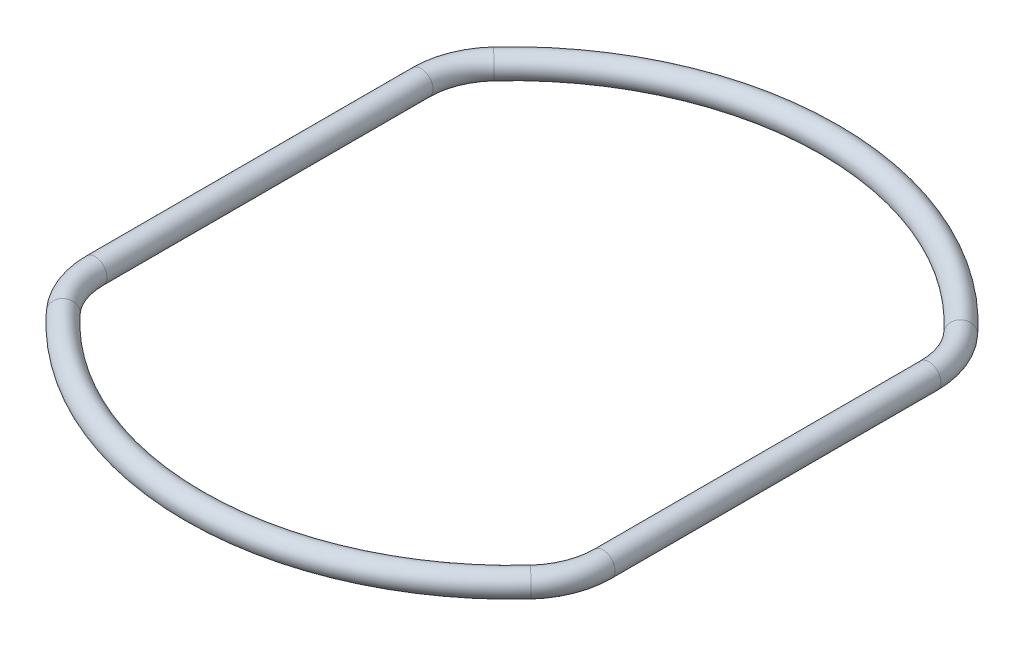
SolidWorks part; units mm, degrees
ref_plane "Vorne" through (0, 0, 0) normal (0, 0, 1) x (1, 0, 0)
ref_plane "Oben" through (0, 0, 0) normal (0, 1, 0) x (1, 0, 0)
ref_plane "Rechts" through (0, 0, 0) normal (1, 0, 0) x (0, 0, -1)
sketch "Skizze1" plane through (0, 0, 0) normal (0, 1, 0) x (1, 0, 0)
  line L0 (0, 82.4427) -> (0, -82.4427) construction
  line L2 (65.9318, -42.3008) -> (65.9318, 42.3008) construction
  line L4 (-65.9318, -42.3008) -> (-65.9318, 42.3008)
  line L5 (65.9318, -49.4954) -> (-65.9318, 49.4954) construction
  line L6 (65.9318, 49.4954) -> (-65.9318, -49.4954) construction
  arc A0 (-60.6434, -55.8495) -> (0, -82.4427) centre (0, 0) ccw
  arc A1 (60.6434, 55.8495) -> (0, 82.4427) centre (0, 0) ccw construction
  arc A2 (-60.6434, -55.8495) -> (-65.9318, -42.3008) centre (-45.9318, -42.3008) cw
  arc A3 (60.6434, -55.8495) -> (65.9318, -42.3008) centre (45.9318, -42.3008) ccw construction
  arc A4 (65.9318, 42.3008) -> (60.6434, 55.8495) centre (45.9318, 42.3008) ccw construction
  arc A5 (-60.6434, 55.8495) -> (-65.9318, 42.3008) centre (-45.9318, 42.3008) ccw
  arc A6 (0, 82.4427) -> (-60.6434, 55.8495) centre (0, 0) ccw
  arc A7 (0, -82.4427) -> (60.6434, -55.8495) centre (0, 0) ccw construction
  point P20 (0, 82.4427)
  point P22 (0, -82.4427)
  dimension "D1" = 20
sketch "Skizze2" plane through (0, 0, 0) normal (1, 0, 0) x (0, 0, -1)
  circle A0 centre (-82.4427, 0) radius 3.1143
sweep "Austragung1" add profiles "Skizze2" path "Skizze1"
mirror "Spiegeln1" about plane through (0, 0, 82.4427) normal (1, 0, 0) of bodies 102
